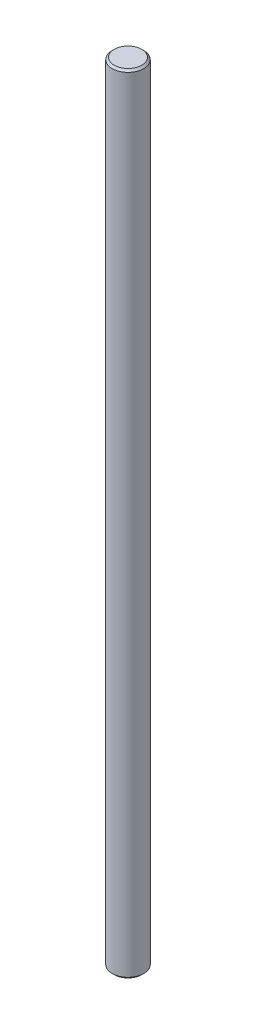
SolidWorks part; units mm, degrees
ref_plane "Front Plane" through (0, 0, 0) normal (0, 0, 1) x (1, 0, 0)
ref_plane "Top Plane" through (0, 0, 0) normal (0, 1, 0) x (1, 0, 0)
ref_plane "Right Plane" through (0, 0, 0) normal (1, 0, 0) x (0, 0, -1)
sketch "Sketch1" plane through (0, 0, 0) normal (0, 1, 0) x (1, 0, 0)
  circle A0 centre (0, 0) radius 2
  dimension "D1" = 4
extrude "Boss-Extrude1" add sketch "Sketch1" along normal mid plane 100
chamfer "Chamfer1" distance 0.25 angle 45 2 edges at (0, -50, 2) (0, 50, 2)
